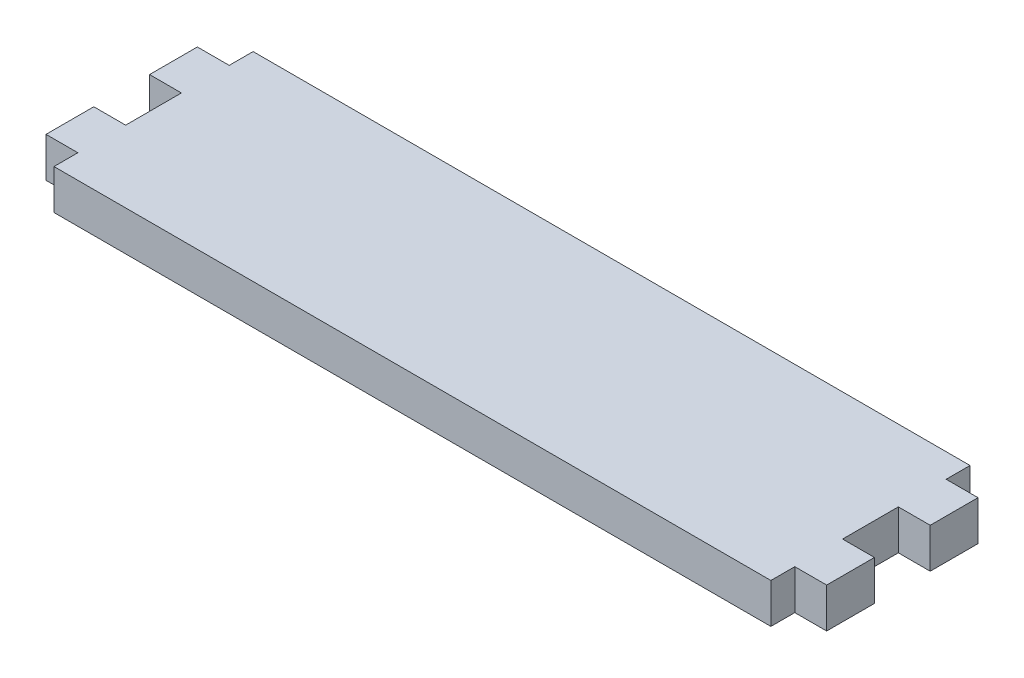
SolidWorks part; units mm, degrees
ref_plane "Front Plane" through (0, 0, 0) normal (0, 0, 1) x (1, 0, 0)
ref_plane "Top Plane" through (0, 0, 0) normal (0, 1, 0) x (1, 0, 0)
ref_plane "Right Plane" through (0, 0, 0) normal (1, 0, 0) x (0, 0, -1)
sketch "Sketch1" plane through (0, 0, 0) normal (0, 1, 0) x (1, 0, 0)
  line L0 (0, 0) -> (0, 3)
  line L1 (0, 3) -> (-4, 3)
  line L2 (-4, 3) -> (-4, 9)
  line L3 (-4, 9) -> (0, 9)
  line L4 (0, 9) -> (0, 16)
  line L5 (0, 16) -> (-4, 16)
  line L6 (-4, 16) -> (-4, 22)
  line L7 (-4, 22) -> (0, 22)
  line L8 (0, 22) -> (0, 25)
  line L9 (0, 25) -> (90, 25)
  line L10 (90, 25) -> (90, 22)
  line L11 (90, 22) -> (94, 22)
  line L12 (94, 22) -> (94, 16)
  line L13 (94, 16) -> (90, 16)
  line L14 (90, 16) -> (90, 9)
  line L15 (90, 9) -> (94, 9)
  line L16 (94, 9) -> (94, 3)
  line L17 (94, 3) -> (90, 3)
  line L18 (90, 3) -> (90, 0)
  line L19 (90, 0) -> (0, 0)
  dimension "D1" = 90
  dimension "D2" = 25
  dimension "D3" = 4
  dimension "D4" = 4
  dimension "D5" = 7
  dimension "D6" = 6
  dimension "D7" = 6
  dimension "D8" = 3
  dimension "D9" = 4
  dimension "D10" = 6
  dimension "D11" = 6
  dimension "D12" = 4
  dimension "D13" = 98
  dimension "D14" = 3
  dimension "D15" = 25
  dimension "D16" = 7
extrude "Boss-Extrude1" add sketch "Sketch1" along normal blind 5
